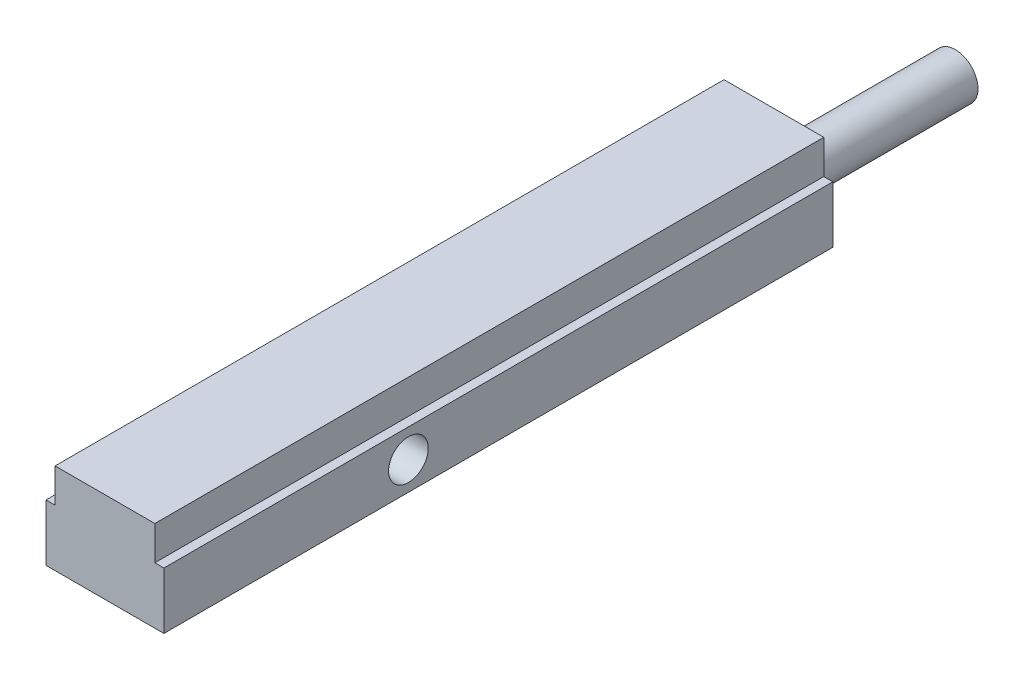
SolidWorks part; units mm, degrees
ref_plane "Front Plane" through (0, 0, 0) normal (0, 0, 1) x (1, 0, 0)
ref_plane "Top Plane" through (0, 0, 0) normal (0, 1, 0) x (1, 0, 0)
ref_plane "Right Plane" through (0, 0, 0) normal (1, 0, 0) x (0, 0, -1)
sketch "Sketch1" plane through (0, 0, 0) normal (0, 0, 1) x (1, 0, 0)
  line L0 (0, -55) -> (0, 55) construction
  line L1 (26, -12.5) -> (-26, -12.5)
  line L2 (26, -12.5) -> (26, 12.5)
  line L3 (26, 12.5) -> (-26, 12.5)
  line L4 (-26, -12.5) -> (-26, 12.5)
  line L5 (26, -12.5) -> (-26, 12.5) construction
  line L6 (26, 12.5) -> (-26, -12.5) construction
  line L7 (0, 12.5) -> (-22, 12.5)
  line L9 (22, 27.5) -> (-22, 27.5)
  line L10 (-22, 12.5) -> (-22, 27.5)
  line L11 (22, 12.5) -> (22, 27.5)
  point P0 (0, 0)
  dimension "D1" = 25
  dimension "D2" = 52
  dimension "D3" = 15
  dimension "D4" = 44
extrude "Boss-Extrude1" add sketch "Sketch1" along normal blind 295 contours L4 L1 L2 L3 | L3 L11 L9 L10
sketch "Sketch3" plane through (0, 0, 0) normal (0, 0, 1) x (1, 0, 0)
  line L0 (0, 33.5749) -> (0, -22.9236) construction
  line L1 (0, -25.3) -> (0, 25.3) construction
  circle A0 centre (0, 0) radius 10
  dimension "D1" = 20
extrude "Boss-Extrude3" add sketch "Sketch3" against normal blind 80
cosmetic thread "Cosmetic Thread2" parameters "D2"=17.252
hole_wizard "M20 Tapped Hole1" positions "Sketch4" profile "Sketch5" tap size "M20" standard "ISO" end condition through all
sketch "Sketch4" plane through (-26, 0, 0) normal (-1, 0, 0) x (0, 0, 1)
  line L0 (295, -12.5) -> (295, 12.5) construction
  point P0 (187.17, 0)
  dimension "D1" = 107.83
sketch "Sketch5" plane through (-26, 0, 187.17) normal (0, 1, 0) x (0, 0, 1)
  line L0 (0, 0) -> (0, 52)
  line L1 (0, 52) -> (8.75, 52)
  line L2 (8.75, 52) -> (8.75, 1.275)
  line L3 (8.75, 1.275) -> (10.025, 0)
  line L5 (10.025, 0) -> (0, 0)
  line L6 (-8.75, 1.275) -> (-10.025, 0) construction
  line L11 (0, -6.35) -> (0, 107.95) construction
  dimension "Thru Tap Drill Dia." = 17.5
  dimension "Thru Tap Drill Depth" = 52
  dimension "Near C'Sink Dia." = 20.05
  dimension "Near C'Sink Angle" = 90
cosmetic thread "Hole Thread1" parameters "D2"=20
